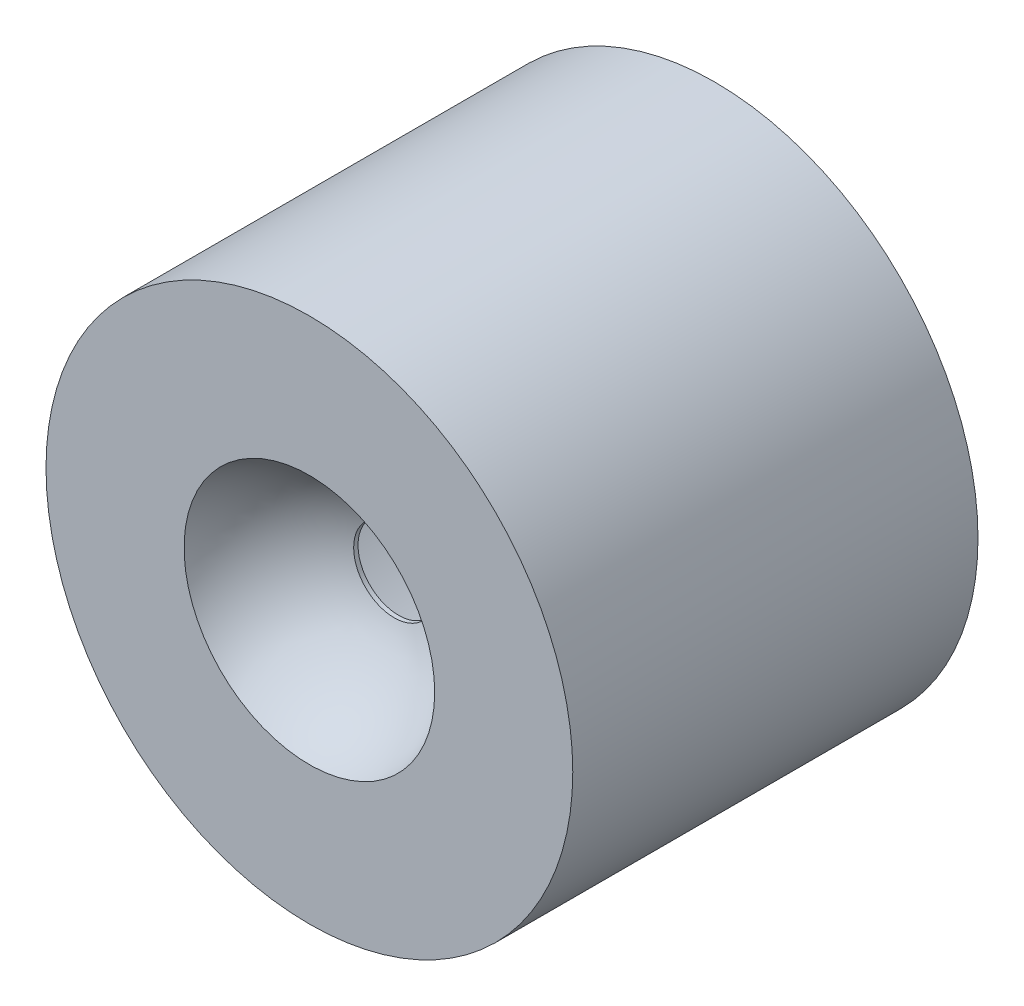
SolidWorks part; units mm, degrees
ref_plane "Front Plane" through (0, 0, 0) normal (0, 0, 1) x (1, 0, 0)
ref_plane "Top Plane" through (0, 0, 0) normal (0, 1, 0) x (1, 0, 0)
ref_plane "Right Plane" through (0, 0, 0) normal (1, 0, 0) x (0, 0, -1)
sketch "Sketch2" plane through (0, 0, 0) normal (0, 0, 1) x (1, 0, 0)
  circle A0 centre (0, 0) radius 32.5
  dimension "D1" = 65
extrude "Boss-Extrude1" add sketch "Sketch2" along normal blind 60
ref_plane "Plane1" through (0, 0, 55) normal (0, 0, 1) x (1, 0, 0)
sketch "Sketch4" plane through (0, 0, 55) normal (0, 0, 1) x (1, 0, 0)
  line L0 (-16.25, 0) -> (16.25, 0)
  line L1 (0, 9.3175) -> (0, -9.8919) construction
  arc A0 (-16.25, 0) -> (16.25, 0) centre (0, 0) cw
  point P6 (0, 0)
  dimension "D1" = 32.5
revolve "Cut-Revolve1" cut sketch "Sketch4" angle 180 about L0
ref_plane "Plane2" through (0, 0, 50) normal (0, 0, 1) x (1, 0, 0)
sketch "Sketch5" plane through (0, 0, 50) normal (0, 0, 1) x (1, 0, 0)
  line L1 (-50.4132, 43.016) -> (47.2177, 43.016)
  line L2 (-50.4132, 43.016) -> (-50.4132, -42.2852)
  line L3 (-50.4132, -42.2852) -> (47.2177, -42.2852)
  line L4 (47.2177, 43.016) -> (47.2177, -42.2852)
extrude "Cut-Extrude1" cut sketch "Sketch5" along normal up to next
sketch "Sketch7" plane through (0, 0, 0) normal (0, 0, -1) x (-1, 0, 0)
  circle A0 centre (0, 0) radius 30
  dimension "D1" = 60
extrude "Cut-Extrude3" cut sketch "Sketch7" against normal blind 39
sketch "Sketch8" plane through (0, 0, 39) normal (0, 0, -1) x (-1, 0, 0)
  line L0 (0, 0) -> (0, -9) construction
  line L1 (0, -9) -> (17.5, -9) construction
  circle A0 centre (17.5, -9) radius 1
  circle A1 centre (-17.5, -9) radius 1
  dimension "D3" = 2
  dimension "D1" = 9
  dimension "D2" = 17.5
extrude "Boss-Extrude2" add sketch "Sketch8" along normal blind 5
sketch "Sketch9" plane through (0, 0, 39) normal (0, 0, -1) x (-1, 0, 0)
  circle A0 centre (0, 0) radius 5
  dimension "D1" = 10
extrude "Cut-Extrude4" cut sketch "Sketch9" against normal blind 1
